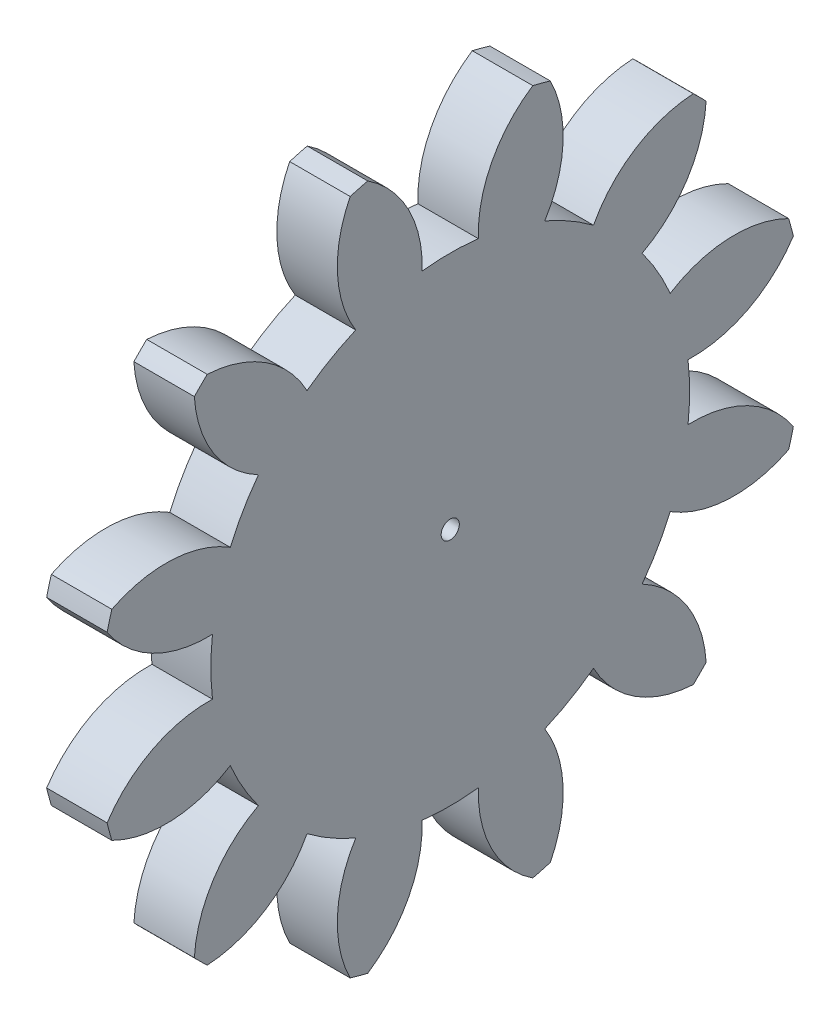
SolidWorks part; units mm, degrees
ref_plane "Plane1" through (0, 0, 0) normal (0, 0, 1) x (1, 0, 0)
ref_plane "Plane2" through (0, 0, 0) normal (0, 1, 0) x (1, 0, 0)
ref_plane "Plane3" through (0, 0, 0) normal (1, 0, 0) x (0, 0, -1)
sketch "HoldingSke" plane through (0, 0, 0) normal (0, 1, 0) x (1, 0, 0)
  line L0 (0, 0) -> (0.3913, -0.0832)
  line L1 (-15, 0) -> (100, 0) construction
  line L2 (0, 0) -> (-2.1039, 2.3779)
  line L3 (0, 0) -> (-11.863, 4.5341)
  line L4 (0, 0) -> (8.4473, 1.7955)
  line L5 (0, 0) -> (-46.8476, -17.4728)
  line L6 (0, 0) -> (-2.4869, -1.6779)
  line L7 (-2.1039, 2.3779) -> (8.6586, 51.2059)
  line L8 (-76.2, 54.61) -> (-76.1, 54.61)
  line L9 (-71.009, 38.7566) -> (-53.1078, 45.2721)
  line L10 (-76.2, 71.12) -> (104.1128, 71.12)
  line L11 (0, 0) -> (-3, 0)
  line L12 (-76.2, 101.6) -> (-76.113, 101.6)
  line L13 (24.9733, 27.94) -> (52.9518, 28.4284)
  line L14 (24.9733, 27.94) -> (24.9743, 27.94)
  line L15 (24.9733, 27.94) -> (100.4006, 29.5858)
  line L16 (-63.627, -2.5) -> (-12.827, -2.5)
  circle A0 centre (0, 0) radius 0.45
  circle A1 centre (0, 0) radius 11.874
  circle A2 centre (0, 0) radius 37.5
  circle A3 centre (0, 0) radius 0.45
  dimension "MHD" = 23.748
  dimension "Hub_dia" = 75
  dimension "Bore" = 0.9
  dimension "MBD" = 0.9
  dimension "Num_teeth" = 12
  dimension "Pitch" = 0.4
  dimension "Overall_len" = 50
  dimension "Show_teeth" = 12
  dimension "Thickness" = 3
  dimension "OAL" = 50.0001
  dimension "T_dim" = 0.1
  dimension "Ap" = 20
  dimension "H" = 19.05
  dimension "Pitch_radius" = 180.3128
  dimension "Width" = 3
  dimension "Backlash" = 0.087
  dimension "Addendum_fac" = 1
  dimension "Dedendum_fac" = 1.25
  dimension "Clearance_fac" = 0.25
  dimension "Dedendum_add" = 0.001
  dimension "Module" = 2.5
sketch "BasProSke" plane through (0, 0, 0) normal (0, 1, 0) x (1, 0, 0)
  line L0 (-10, 0) -> (60, 0) construction
  line L1 (0, 0) -> (0, 17.5)
  line L2 (0, 0) -> (3, 0)
  line L3 (3, 0) -> (3, 17.5)
  line L4 (3, 17.5) -> (0, 17.5)
  dimension "Thickness" = 3
  dimension "Diameter" = 35
revolve "Base-Revolve" add sketch "BasProSke" angle 360 about L0
sketch "TooCutSke" plane through (0, 0, 0) normal (1, 0, 0) x (0, 0, -1)
  line L1 (0, 0) -> (0, 107) construction
  line L2 (0, 0) -> (-2.1099, 14.8509) construction
  line L3 (0, 0) -> (-7.7081, 28.7671) construction
  line L4 (-2.1099, 14.8509) -> (-3.8541, 14.3835) construction
  arc A0 (1.3944, 11.7918) -> (-1.3944, 11.7918) centre (0, 0) ccw
  arc A1 (4.1219, 17.0338) -> (-4.1219, 17.0338) centre (0, 0) ccw
  circle A2 centre (0, 0) radius 15 construction
  circle A3 centre (0, 0) radius 14.0954 construction
  arc A4 (-1.3944, 11.7918) -> (-4.1219, 17.0338) centre (-7.3907, 12.0024) ccw
  arc A5 (4.1219, 17.0338) -> (1.3944, 11.7918) centre (7.3907, 12.0024) ccw
  dimension "Root_dia" = 23.748
  dimension "Overcut_dia" = 35.0508
  dimension "Pitch_dia" = 30
  dimension "Base_dia" = 28.1908
  dimension "Flank_rad" = 6
  dimension "Half_ang" = 15
  dimension "Half_CT" = 1.8056
extrude "ToothCut" cut sketch "TooCutSke" along normal through all
fillet "Breaks" [suppressed] radius 0.05
fillet "RootFillets" [suppressed] radius 0.626
pattern_circular "TeethCuts" count 12 every 30 about axis through (-10, 0, 0) along (1, 0, 0) of "ToothCut", "RootFillets", "Breaks"
sketch "HubNeaOneSke" plane through (0, 0, 0) normal (-1, 0, 0) x (0, 0, 1)
  circle A0 centre (0, 0) radius 11.874
  dimension "Diameter" = 23.748
extrude "HubNearOne" [suppressed] add sketch "HubNeaOneSke" along normal blind 47.0001
sketch "HubNeaBotSke" plane through (0, 0, 0) normal (-1, 0, 0) x (0, 0, 1)
  circle A0 centre (0, 0) radius 11.874
  dimension "Diameter" = 23.748
extrude "HubNearBoth" [suppressed] add sketch "HubNeaBotSke" along normal blind 23.5
ref_plane "FarPln" through (3, 0, 0) normal (1, 0, 0) x (0, 0, -1)
sketch "HubFarSke" plane through (3, 0, 0) normal (1, 0, 0) x (0, 0, -1)
  circle A0 centre (0, 0) radius 11.874
  dimension "Diameter" = 23.748
extrude "HubFar" [suppressed] add sketch "HubFarSke" along normal blind 23.5
sketch "BorSke" plane through (0, 0, 0) normal (1, 0, 0) x (0, 0, -1)
  circle A0 centre (0, 0) radius 0.45
  dimension "Diameter" = 0.9
extrude "Bore" cut sketch "BorSke" along normal mid plane 100.0001
sketch "KeySke" plane through (0, 0, 0) normal (1, 0, 0) x (0, 0, -1)
  line L0 (-0.05, 0) -> (-0.05, 0.55)
  line L1 (-0.05, 0.55) -> (0.05, 0.55)
  line L2 (0.05, 0.55) -> (0.05, 0)
  line L3 (0, 0) -> (0, 34) construction
  line L4 (-0.05, 0) -> (0.05, 0)
  dimension "Offset" = 0.55
  dimension "Width" = 0.1
extrude "Keyway" [suppressed] cut sketch "KeySke" along normal mid plane 100.0001
pattern_circular "Keyway2" [suppressed] count 2 every 90 about axis through (-10, 0, 0) along (1, 0, 0)
equation "' \"Module@HoldingSke\" = 6.35"
equation "' \"Num_teeth@HoldingSke\" = 12"
equation "' \"Ap@HoldingSke\" =  20"
equation "' \"Ap@HoldingSke\" = 20"
equation "' \"Width@HoldingSke\" = 0.5 * 25.4"
equation "' \"Hub_dia@HoldingSke\"= 1 * 25.4"
equation "' \"Hub_dia@HoldingSke\" = 1 * 25.4"
equation "' \"Overall_len@HoldingSke\" = 1.0 * 25.4"
equation "' \"Bore@HoldingSke\" = 0.75 * 25.4"
equation "' \"T_dim@HoldingSke\" = 0.1 * 25.4"
equation "' \"Width@KeySke\" = 0.25 * 25.4"
equation "' \"Show_teeth@HoldingSke\" = 13"
equation "' \"Backlash@HoldingSke\" = 0.009 * 25.4"
equation "' \"Addendum_fac@HoldingSke\" = 1.0"
equation "' \"Dedendum_fac@HoldingSke\" = 1.25"
equation "' \"Dedendum_add@HoldingSke\" = 0.00005 * 25.4"
equation "' \"Clearance_fac@HoldingSke\" = 0.25"
equation "\"Pitch@HoldingSke\" = 1 / \"Module@HoldingSke\""
equation "\"Overcut_dia@TooCutSke\" = (\"Num_teeth@HoldingSke\" + 2 * \"Addendum_fac@HoldingSke\") / \"Pitch@HoldingSke\" + 0.002 * 25.4"
equation "\"Pitch_dia@TooCutSke\" = \"Num_teeth@HoldingSke\" / \"Pitch@HoldingSke\""
equation "\"Base_dia@TooCutSke\" = \"Num_teeth@HoldingSke\" / \"Pitch@HoldingSke\" * cos((\"Ap@HoldingSke\"  * 3.14159265 / 180))"
equation "\"Root_dia@TooCutSke\" = (\"Num_teeth@HoldingSke\" + 2) / \"Pitch@HoldingSke\" - 2 * (\"Addendum_fac@HoldingSke\" + \"Dedendum_fac@HoldingSke\") / \"Pitch@HoldingSke\" - \"Dedendum_add@HoldingSke\" * 2"
equation "\"Half_ang@TooCutSke\" = 180 / \"Num_teeth@HoldingSke\""
equation "\"Half_CT@TooCutSke\" = \"Num_teeth@HoldingSke\" / \"Pitch@HoldingSke\" * sin((3.14159265 / 2 / \"Num_teeth@HoldingSke\")) / 2 - 7 * \"Backlash@HoldingSke\" / 4"
equation "\"Flank_rad@TooCutSke\" = \"Num_teeth@HoldingSke\" / \"Pitch@HoldingSke\" / 5"
equation "\"Radius@RootFillets\" = \"Clearance_fac@HoldingSke\" / \"Pitch@HoldingSke\" + \"Dedendum_add@HoldingSke\""
equation "\"Break_rad@Breaks\" = 0.02 / \"Pitch@HoldingSke\""
equation "\"Thickness@HoldingSke\" = \"Width@HoldingSke\""
equation "\"OAL@HoldingSke\" = \"Thickness@HoldingSke\""
equation "\"MHD@HoldingSke\" = (\"Num_teeth@HoldingSke\" + 2) / \"Pitch@HoldingSke\" - 2 * (\"Addendum_fac@HoldingSke\" + \"Dedendum_fac@HoldingSke\")  / \"Pitch@HoldingSke\" - \"Dedendum_add@HoldingSke\" * 2"
equation "\"MBD@HoldingSke\" = (\"Num_teeth@HoldingSke\" + 2) / \"Pitch@HoldingSke\" - 2 * (\"Addendum_fac@HoldingSke\" + \"Dedendum_fac@HoldingSke\")  / \"Pitch@HoldingSke\" - \"Dedendum_add@HoldingSke\" * 2 - 0.002 * 25.4"
equation "\"MHD@HoldingSke\" = ((sgn( \"MHD@HoldingSke\" - \"Hub_dia@HoldingSke\" )-1)*( \"MHD@HoldingSke\" - \"Hub_dia@HoldingSke\" ))/-2+ \"Hub_dia@HoldingSke\""
equation "\"MBD@HoldingSke\" = ((sgn( \"MBD@HoldingSke\" - \"Bore@HoldingSke\" )-1)*( \"MBD@HoldingSke\" - \"Bore@HoldingSke\" ))/-2+ \"Bore@HoldingSke\""
equation "\"OAL@HoldingSke\" = ((sgn( \"OAL@HoldingSke\" - \"Overall_len@HoldingSke\" )+1)*( \"OAL@HoldingSke\" - \"Overall_len@HoldingSke\" ))/2 + \"Overall_len@HoldingSke\" + 0.000002 * 25.4"
equation "\"Num_teeth@TeethCuts\" = int( \"Show_teeth@HoldingSke\" ) + 1"
equation "\"Num_teeth@TeethCuts\" = ((sgn( \"Num_teeth@TeethCuts\" - \"Num_teeth@HoldingSke\" )-1)*( \"Num_teeth@TeethCuts\" - \"Num_teeth@HoldingSke\" ))/-2+ \"Num_teeth@HoldingSke\""
equation "\"Num_teeth@TeethCuts\" = ((sgn( \"Num_teeth@TeethCuts\" - 2.0)+1)*( \"Num_teeth@TeethCuts\" - 2.0))/2 +2.0"
equation "\"Angle@TeethCuts\" = 360.0 / \"Num_teeth@HoldingSke\""
equation "\"Diameter@BasProSke\" = (\"Num_teeth@HoldingSke\" + 2 * \"Addendum_fac@HoldingSke\") / \"Pitch@HoldingSke\""
equation "\"Thickness@BasProSke\"  = \"Thickness@HoldingSke\""
equation "' \"Fillet_rad@BasProSke\" =  \"Thickness@HoldingSke\" * 0.05"
equation "' \"Fillet_rad@BasProSke\" = \"Thickness@HoldingSke\" * 0.05"
equation "\"MHD@HoldingSke\" = ((sgn( \"MHD@HoldingSke\" - \"Root_dia@TooCutSke\" )-1)*( \"MHD@HoldingSke\" - \"Root_dia@TooCutSke\" ))/-2+ \"Root_dia@TooCutSke\""
equation "\"Diameter@HubNeaOneSke\" = \"MHD@HoldingSke\""
equation "\"Length@HubNearOne\" = \"OAL@HoldingSke\" - \"Thickness@BasProSke\""
equation "\"Diameter@HubNeaBotSke\" = \"MHD@HoldingSke\""
equation "\"Length@HubNearBoth\" = ( \"OAL@HoldingSke\" - \"Thickness@BasProSke\" ) / 2.0"
equation "\"Thickness@FarPln\" = \"Thickness@BasProSke\""
equation "\"Diameter@HubFarSke\" = \"MHD@HoldingSke\""
equation "\"Length@HubFar\" = ( \"OAL@HoldingSke\" - \"Thickness@BasProSke\" ) / 2.0"
equation "\"Diameter@BorSke\" = \"MBD@HoldingSke\""
equation "\"D1@Bore\" = \"OAL@HoldingSke\" * 2.0"
equation "\"D1@Keyway\" = \"OAL@HoldingSke\" * 2.0"
equation "\"Offset@KeySke\" = \"T_dim@HoldingSke\" + \"MBD@HoldingSke\" / 2.0"
